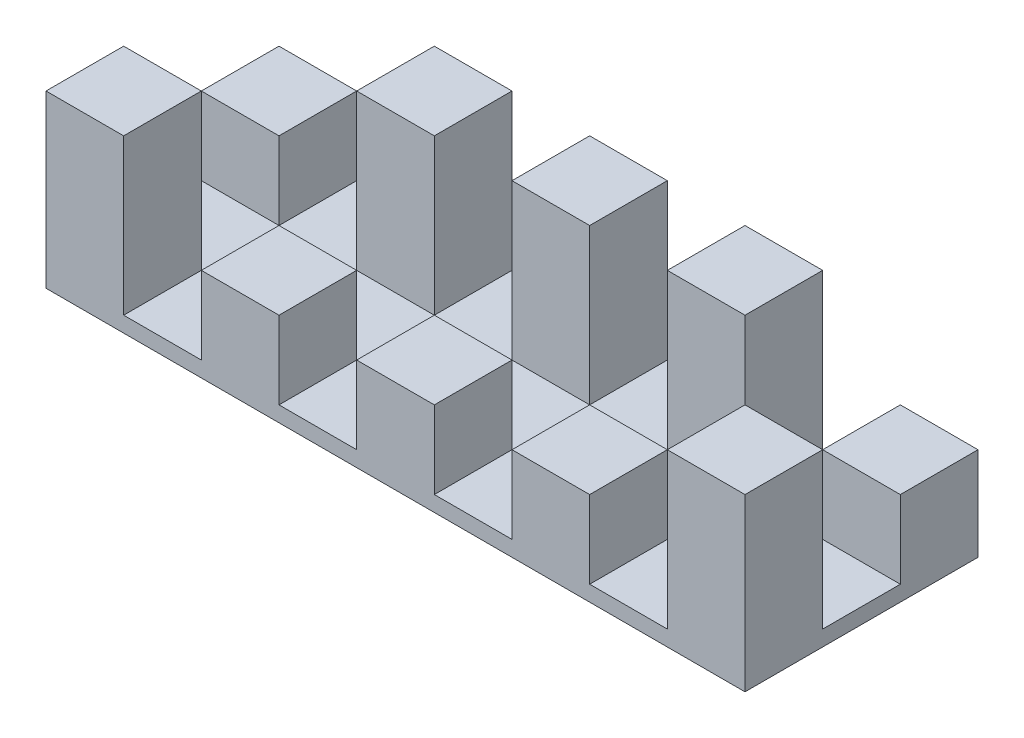
SolidWorks part; units mm, degrees
ref_plane "Front Plane" through (0, 0, 0) normal (0, 0, 1) x (1, 0, 0)
ref_plane "Top Plane" through (0, 0, 0) normal (0, 1, 0) x (1, 0, 0)
ref_plane "Right Plane" through (0, 0, 0) normal (1, 0, 0) x (0, 0, -1)
sketch "Sketch3" plane through (0, 0, 0) normal (0, 1, 0) x (1, 0, 0)
  line L1 (-225, 75) -> (225, 75)
  line L2 (-225, 75) -> (-225, -75)
  line L3 (-225, -75) -> (225, -75)
  line L4 (225, 75) -> (225, -75)
  line L5 (-225, 75) -> (225, -75) construction
  line L6 (-225, -75) -> (225, 75) construction
  point P0 (0, 0)
  dimension "D1" = 450
  dimension "D2" = 150
extrude "Boss-Extrude1" add sketch "Sketch3" along normal blind 10
sketch "Sketch12" plane through (0, 10, 0) normal (0, 1, 0) x (1, 0, 0)
  line L0 (-25, -75) -> (25, -75)
  line L5 (225, 75) -> (175, 75)
  line L6 (225, 75) -> (225, 25)
  line L7 (225, 25) -> (175, 25)
  line L8 (175, 75) -> (175, 25)
  line L13 (-25, -75) -> (-25, -25)
  line L27 (75, -75) -> (125, -75)
  line L28 (-25, -25) -> (25, -25)
  line L29 (25, -75) -> (25, -25)
  line L34 (-225, -75) -> (225, -75) construction
  line L35 (-225, 75) -> (-175, 75)
  line L36 (-225, 75) -> (-225, 25)
  line L37 (-225, 25) -> (-175, 25)
  line L38 (-175, 75) -> (-175, 25)
  line L39 (-125, -75) -> (-75, -75)
  line L40 (-125, -75) -> (-125, -25)
  line L41 (-125, -25) -> (-75, -25)
  line L42 (-75, -75) -> (-75, -25)
  line L43 (-225, 75) -> (-225, -75) construction
  line L44 (75, -75) -> (75, -25)
  line L45 (75, -25) -> (125, -25)
  line L46 (125, -75) -> (125, -25)
  dimension "D1" = 50
  dimension "D2" = 50
  dimension "D3" = 50
  dimension "D4" = 50
  dimension "D5" = 50
  dimension "D6" = 100
  dimension "D7" = 50
  dimension "D8" = 50
  dimension "D9" = 50
  dimension "D10" = 50
  dimension "D11" = 50
  dimension "D12" = 50
  dimension "D13" = 50
  dimension "D14" = 50
  dimension "D15" = 50
extrude "Boss-Extrude2" add sketch "Sketch12" along normal blind 50
sketch "Sketch14" plane through (0, 10, 0) normal (0, 1, 0) x (1, 0, 0)
  line L0 (175, 75) -> (-175, 75) construction
  line L1 (-225, -75) -> (-175, -75)
  line L2 (-225, -75) -> (-225, -25)
  line L3 (-225, -25) -> (-175, -25)
  line L4 (-175, -75) -> (-175, -25)
  line L5 (225, -75) -> (175, -75)
  line L6 (225, -75) -> (225, -25)
  line L7 (225, -25) -> (175, -25)
  line L8 (175, -75) -> (175, -25)
  line L9 (-125, 25) -> (-75, 25)
  line L10 (-125, 25) -> (-125, 75)
  line L11 (-125, 75) -> (-75, 75)
  line L12 (-75, 25) -> (-75, 75)
  line L14 (-25, 25) -> (25, 25)
  line L15 (-25, 25) -> (-25, 75)
  line L16 (-25, 75) -> (25, 75)
  line L17 (25, 25) -> (25, 75)
  line L18 (75, 25) -> (125, 25)
  line L19 (75, 25) -> (75, 75)
  line L20 (75, 75) -> (125, 75)
  line L21 (125, 25) -> (125, 75)
extrude "Boss-Extrude3" add sketch "Sketch14" along normal blind 100
